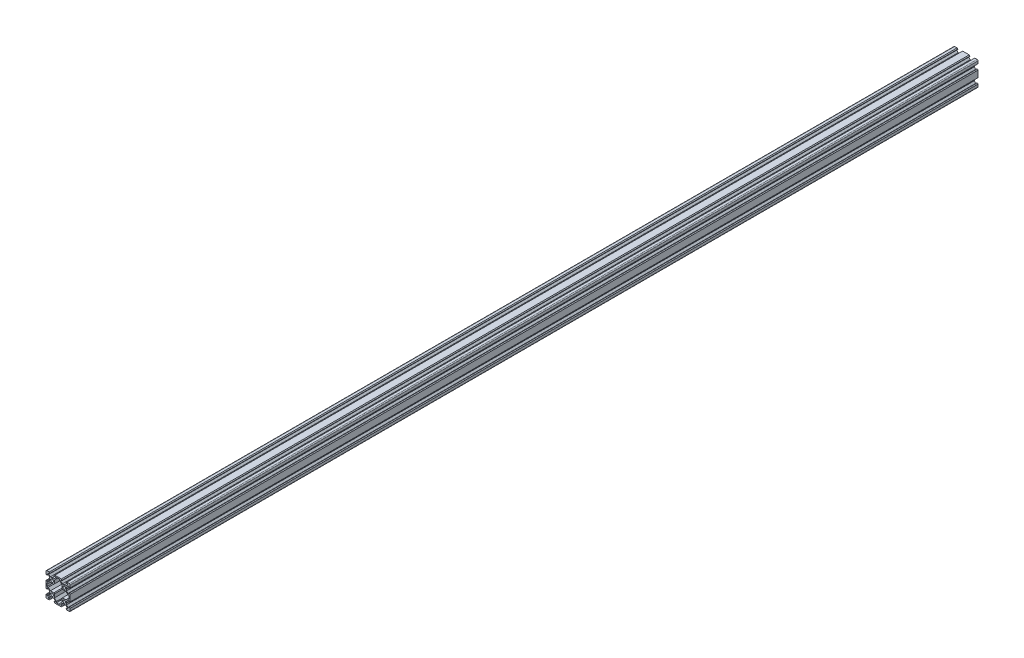
SolidWorks part; units mm, degrees
material "6061-T6 (SS)"
ref_plane "Front Plane" through (0, 0, 0) normal (0, 0, 1) x (1, 0, 0)
ref_plane "Top Plane" through (0, 0, 0) normal (0, 1, 0) x (1, 0, 0)
ref_plane "Right Plane" through (0, 0, 0) normal (1, 0, 0) x (0, 0, -1)
sketch "Sketch1" plane through (0, 0, 0) normal (0, 0, 1) x (1, 0, 0)
  line L1 (18.5, -20) -> (-18.5, -20)
  line L2 (20, -18.5) -> (20, 18.5)
  line L3 (18.5, 20) -> (-18.5, 20)
  line L4 (-20, -18.5) -> (-20, 18.5)
  line L5 (20, -20) -> (-20, 20) construction
  line L6 (20, 20) -> (-20, -20) construction
  circle A0 centre (-10, 10) radius 2.3
  circle A1 centre (10, -10) radius 2.3
  circle A2 centre (10, 10) radius 2.3
  circle A3 centre (-10, -10) radius 2.3
  arc A4 (-18.5, -20) -> (-20, -18.5) centre (-18.5, -18.5) cw
  arc A5 (18.5, -20) -> (20, -18.5) centre (18.5, -18.5) ccw
  arc A6 (20, 18.5) -> (18.5, 20) centre (18.5, 18.5) ccw
  arc A7 (-18.5, 20) -> (-20, 18.5) centre (-18.5, 18.5) ccw
  point P0 (0, 0)
  line B0 (-10, 10) -> (-10, 20) construction
  line B1 (-10, 13.69) -> (-10.21, 13.9)
  line B2 (-10.21, 13.9) -> (-12.8393, 13.9)
  line B3 (-12.8393, 13.9) -> (-15.5, 16.5607)
  line B4 (-15.5, 16.5607) -> (-15.5, 18.2)
  line B5 (-15.5, 18.2) -> (-13.395, 18.2)
  line B6 (-13.395, 18.2) -> (-13.395, 18.815)
  line B7 (-13.395, 18.815) -> (-14.58, 20)
  line B8 (-14.58, 20) -> (-5.42, 20)
  line B9 (-10, 10) -> (-15.9132, 15.9132) construction
  line B10 (-6.605, 18.815) -> (-5.42, 20)
  line B11 (-6.605, 18.2) -> (-6.605, 18.815)
  line B12 (-4.5, 18.2) -> (-6.605, 18.2)
  line B13 (-4.5, 16.5607) -> (-4.5, 18.2)
  line B14 (-7.1607, 13.9) -> (-4.5, 16.5607)
  line B15 (-9.79, 13.9) -> (-7.1607, 13.9)
  line B16 (-10, 13.69) -> (-9.79, 13.9)
  line B17 (10, 10) -> (10, 20) construction
  line B18 (10, 13.69) -> (9.79, 13.9)
  line B19 (9.79, 13.9) -> (7.1607, 13.9)
  line B20 (7.1607, 13.9) -> (4.5, 16.5607)
  line B21 (4.5, 16.5607) -> (4.5, 18.2)
  line B22 (4.5, 18.2) -> (6.605, 18.2)
  line B23 (6.605, 18.2) -> (6.605, 18.815)
  line B24 (6.605, 18.815) -> (5.42, 20)
  line B25 (5.42, 20) -> (14.58, 20)
  line B26 (10, 10) -> (4.0868, 15.9132) construction
  line B27 (13.395, 18.815) -> (14.58, 20)
  line B28 (13.395, 18.2) -> (13.395, 18.815)
  line B29 (15.5, 18.2) -> (13.395, 18.2)
  line B30 (15.5, 16.5607) -> (15.5, 18.2)
  line B31 (12.8393, 13.9) -> (15.5, 16.5607)
  line B32 (10.21, 13.9) -> (12.8393, 13.9)
  line B33 (10, 13.69) -> (10.21, 13.9)
  line B34 (-10, 10) -> (-20, 10) construction
  line B35 (-13.69, 10) -> (-13.9, 9.79)
  line B36 (-13.9, 9.79) -> (-13.9, 7.1607)
  line B37 (-13.9, 7.1607) -> (-16.5607, 4.5)
  line B38 (-16.5607, 4.5) -> (-18.2, 4.5)
  line B39 (-18.2, 4.5) -> (-18.2, 6.605)
  line B40 (-18.2, 6.605) -> (-18.815, 6.605)
  line B41 (-18.815, 6.605) -> (-20, 5.42)
  line B42 (-20, 5.42) -> (-20, 14.58)
  line B43 (-10, 10) -> (-15.9132, 4.0868) construction
  line B44 (-18.815, 13.395) -> (-20, 14.58)
  line B45 (-18.2, 13.395) -> (-18.815, 13.395)
  line B46 (-18.2, 15.5) -> (-18.2, 13.395)
  line B47 (-16.5607, 15.5) -> (-18.2, 15.5)
  line B48 (-13.9, 12.8393) -> (-16.5607, 15.5)
  line B49 (-13.9, 10.21) -> (-13.9, 12.8393)
  line B50 (-13.69, 10) -> (-13.9, 10.21)
  line B51 (-10, -10) -> (-20, -10) construction
  line B52 (-13.69, -10) -> (-13.9, -10.21)
  line B53 (-13.9, -10.21) -> (-13.9, -12.8393)
  line B54 (-13.9, -12.8393) -> (-16.5607, -15.5)
  line B55 (-16.5607, -15.5) -> (-18.2, -15.5)
  line B56 (-18.2, -15.5) -> (-18.2, -13.395)
  line B57 (-18.2, -13.395) -> (-18.815, -13.395)
  line B58 (-18.815, -13.395) -> (-20, -14.58)
  line B59 (-20, -14.58) -> (-20, -5.42)
  line B60 (-10, -10) -> (-15.9132, -15.9132) construction
  line B61 (-18.815, -6.605) -> (-20, -5.42)
  line B62 (-18.2, -6.605) -> (-18.815, -6.605)
  line B63 (-18.2, -4.5) -> (-18.2, -6.605)
  line B64 (-16.5607, -4.5) -> (-18.2, -4.5)
  line B65 (-13.9, -7.1607) -> (-16.5607, -4.5)
  line B66 (-13.9, -9.79) -> (-13.9, -7.1607)
  line B67 (-13.69, -10) -> (-13.9, -9.79)
  line B68 (-10, -10) -> (-10, -20) construction
  line B69 (-10, -13.69) -> (-9.79, -13.9)
  line B70 (-9.79, -13.9) -> (-7.1607, -13.9)
  line B71 (-7.1607, -13.9) -> (-4.5, -16.5607)
  line B72 (-4.5, -16.5607) -> (-4.5, -18.2)
  line B73 (-4.5, -18.2) -> (-6.605, -18.2)
  line B74 (-6.605, -18.2) -> (-6.605, -18.815)
  line B75 (-6.605, -18.815) -> (-5.42, -20)
  line B76 (-5.42, -20) -> (-14.58, -20)
  line B77 (-10, -10) -> (-4.0868, -15.9132) construction
  line B78 (-13.395, -18.815) -> (-14.58, -20)
  line B79 (-13.395, -18.2) -> (-13.395, -18.815)
  line B80 (-15.5, -18.2) -> (-13.395, -18.2)
  line B81 (-15.5, -16.5607) -> (-15.5, -18.2)
  line B82 (-12.8393, -13.9) -> (-15.5, -16.5607)
  line B83 (-10.21, -13.9) -> (-12.8393, -13.9)
  line B84 (-10, -13.69) -> (-10.21, -13.9)
  line B85 (10, -10) -> (10, -20) construction
  line B86 (10, -13.69) -> (10.21, -13.9)
  line B87 (10.21, -13.9) -> (12.8393, -13.9)
  line B88 (12.8393, -13.9) -> (15.5, -16.5607)
  line B89 (15.5, -16.5607) -> (15.5, -18.2)
  line B90 (15.5, -18.2) -> (13.395, -18.2)
  line B91 (13.395, -18.2) -> (13.395, -18.815)
  line B92 (13.395, -18.815) -> (14.58, -20)
  line B93 (14.58, -20) -> (5.42, -20)
  line B94 (10, -10) -> (15.9132, -15.9132) construction
  line B95 (6.605, -18.815) -> (5.42, -20)
  line B96 (6.605, -18.2) -> (6.605, -18.815)
  line B97 (4.5, -18.2) -> (6.605, -18.2)
  line B98 (4.5, -16.5607) -> (4.5, -18.2)
  line B99 (7.1607, -13.9) -> (4.5, -16.5607)
  line B100 (9.79, -13.9) -> (7.1607, -13.9)
  line B101 (10, -13.69) -> (9.79, -13.9)
  line B102 (10, 10) -> (20, 10) construction
  line B103 (13.69, 10) -> (13.9, 10.21)
  line B104 (13.9, 10.21) -> (13.9, 12.8393)
  line B105 (13.9, 12.8393) -> (16.5607, 15.5)
  line B106 (16.5607, 15.5) -> (18.2, 15.5)
  line B107 (18.2, 15.5) -> (18.2, 13.395)
  line B108 (18.2, 13.395) -> (18.815, 13.395)
  line B109 (18.815, 13.395) -> (20, 14.58)
  line B110 (20, 14.58) -> (20, 5.42)
  line B111 (10, 10) -> (15.9132, 15.9132) construction
  line B112 (18.815, 6.605) -> (20, 5.42)
  line B113 (18.2, 6.605) -> (18.815, 6.605)
  line B114 (18.2, 4.5) -> (18.2, 6.605)
  line B115 (16.5607, 4.5) -> (18.2, 4.5)
  line B116 (13.9, 7.1607) -> (16.5607, 4.5)
  line B117 (13.9, 9.79) -> (13.9, 7.1607)
  line B118 (13.69, 10) -> (13.9, 9.79)
  line B119 (10, -10) -> (20, -10) construction
  line B120 (13.69, -10) -> (13.9, -9.79)
  line B121 (13.9, -9.79) -> (13.9, -7.1607)
  line B122 (13.9, -7.1607) -> (16.5607, -4.5)
  line B123 (16.5607, -4.5) -> (18.2, -4.5)
  line B124 (18.2, -4.5) -> (18.2, -6.605)
  line B125 (18.2, -6.605) -> (18.815, -6.605)
  line B126 (18.815, -6.605) -> (20, -5.42)
  line B127 (20, -5.42) -> (20, -14.58)
  line B128 (10, -10) -> (15.9132, -4.0868) construction
  line B129 (18.815, -13.395) -> (20, -14.58)
  line B130 (18.2, -13.395) -> (18.815, -13.395)
  line B131 (18.2, -15.5) -> (18.2, -13.395)
  line B132 (16.5607, -15.5) -> (18.2, -15.5)
  line B133 (13.9, -12.8393) -> (16.5607, -15.5)
  line B134 (13.9, -10.21) -> (13.9, -12.8393)
  line B135 (13.69, -10) -> (13.9, -10.21)
  line B136 (-18.2, -2.7) -> (-18.2, 2.7)
  line B137 (-18.2, 2.7) -> (-16.2393, 2.7)
  line B138 (-16.2393, 2.7) -> (-12.8393, 6.1)
  line B139 (-12.8393, 6.1) -> (-7.1607, 6.1)
  line B140 (-10, 6.1) -> (-10, 0) construction
  line B141 (-10, 0) -> (-18.2, 0) construction
  line B142 (-12.8393, -6.1) -> (-7.1607, -6.1)
  line B143 (-16.2393, -2.7) -> (-12.8393, -6.1)
  line B144 (-18.2, -2.7) -> (-16.2393, -2.7)
  line B145 (-10, 6.1) -> (-10, 10) construction
  line B146 (-10, 10) -> (-15.0927, 4.9073) construction
  line B147 (-10, 10) -> (-6.3747, 6.3747) construction
  line B148 (2.7, 18.2) -> (2.7, 16.2393)
  line B149 (2.7, 16.2393) -> (6.1, 12.8393)
  line B150 (6.1, 12.8393) -> (6.1, 7.1607)
  line B151 (-6.1, 12.8393) -> (-6.1, 7.1607)
  line B152 (-2.7, 16.2393) -> (-6.1, 12.8393)
  line B153 (-2.7, 18.2) -> (-2.7, 16.2393)
  line B154 (2.7, 18.2) -> (-2.7, 18.2)
  line B155 (2.7, -18.2) -> (-2.7, -18.2)
  line B156 (-2.7, -18.2) -> (-2.7, -16.2393)
  line B157 (-2.7, -16.2393) -> (-6.1, -12.8393)
  line B158 (-6.1, -12.8393) -> (-6.1, -7.1607)
  line B159 (6.1, -12.8393) -> (6.1, -7.1607)
  line B160 (2.7, -16.2393) -> (6.1, -12.8393)
  line B161 (2.7, -18.2) -> (2.7, -16.2393)
  line B162 (0, 18.2) -> (0, -18.2) construction
  line B163 (12.8393, -6.1) -> (7.1607, -6.1)
  line B164 (16.2393, -2.7) -> (12.8393, -6.1)
  line B165 (18.2, -2.7) -> (16.2393, -2.7)
  line B166 (18.2, -2.7) -> (18.2, 2.7)
  line B167 (18.2, 2.7) -> (16.2393, 2.7)
  line B168 (16.2393, 2.7) -> (12.8393, 6.1)
  line B169 (12.8393, 6.1) -> (7.1607, 6.1)
  line B170 (-7.1607, 6.1) -> (-6.1, 7.1607)
  line B171 (6.1, 7.1607) -> (7.1607, 6.1)
  line B172 (7.1607, -6.1) -> (6.1, -7.1607)
  line B173 (-6.1, -7.1607) -> (-7.1607, -6.1)
  dimension "D4" = 4.6
  dimension "D5" = 1.5
  dimension "D1" = 40
  dimension "D2" = 10
  dimension "D3" = 10
sketch_block_instance "V Slot 2-1"
sketch_block "V Slot 2" parameters "D1"=10, "D2"=11, "D3"=4.3, "D4"=1.8, "D5"=0.21, "D6"=45, "D7"=9.16, "D8"=1.5, "D9"=6.79
sketch_block_instance "V Slot 2-2"
sketch_block_instance "V Slot 2-3"
sketch_block_instance "V Slot 2-4"
sketch_block_instance "V Slot 2-5"
sketch_block_instance "V Slot 2-6"
sketch_block_instance "V Slot 2-7"
sketch_block_instance "V Slot 2-8"
sketch_block_instance "Center Cutout 2-1"
sketch_block "Center Cutout 2" parameters "D1"=5.4, "D2"=12.2, "D3"=8.2, "D4"=45, "D5"=10, "D6"=1.5
extrude "Boss-Extrude1" add sketch "Sketch1" along normal blind 1500 contours B135 B120 B121 B122 B123 B124 B125 B126 L2 B112 B113 B114 B115 B116 B117 B118 B103 B104 B105 B106 B107 B108 B109 A6 L3 B27 B28 B29 B30 B31 B32 B33 B18 B19 B20 B21 B22 B23 B24 B10 B11 B12 B13 B14 B15 B16 B1 B2 B3
